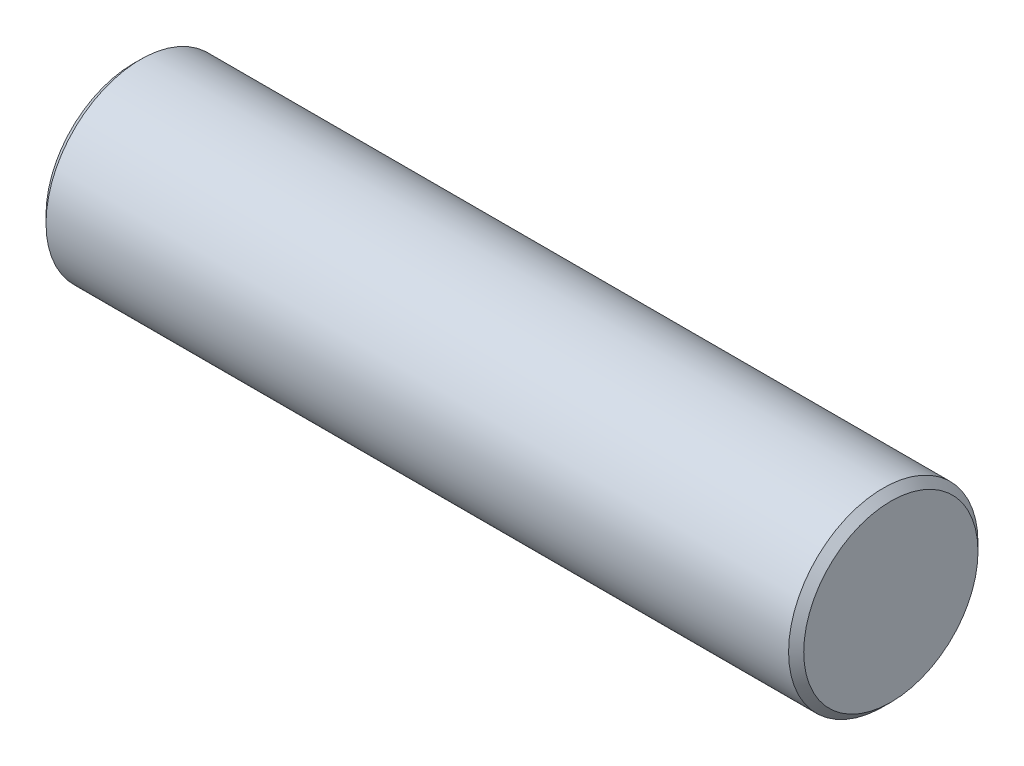
SolidWorks part; units mm, degrees
ref_plane "Front" through (0, 0, 0) normal (0, 0, 1) x (1, 0, 0)
ref_plane "Top" through (0, 0, 0) normal (0, 1, 0) x (1, 0, 0)
ref_plane "Right" through (0, 0, 0) normal (1, 0, 0) x (0, 0, -1)
sketch "xsection" plane through (0, 0, 0) normal (1, 0, 0) x (0, 0, -1)
  circle A0 centre (0, 0) radius 3.175
  dimension "diameter" = 6.35
extrude "extrusion" add sketch "xsection" along normal mid plane 25.4
chamfer "Chamfer1" distance 0.254 angle 45 2 edges at (-12.7, 0, -3.175) (12.7, 0, -3.175)
